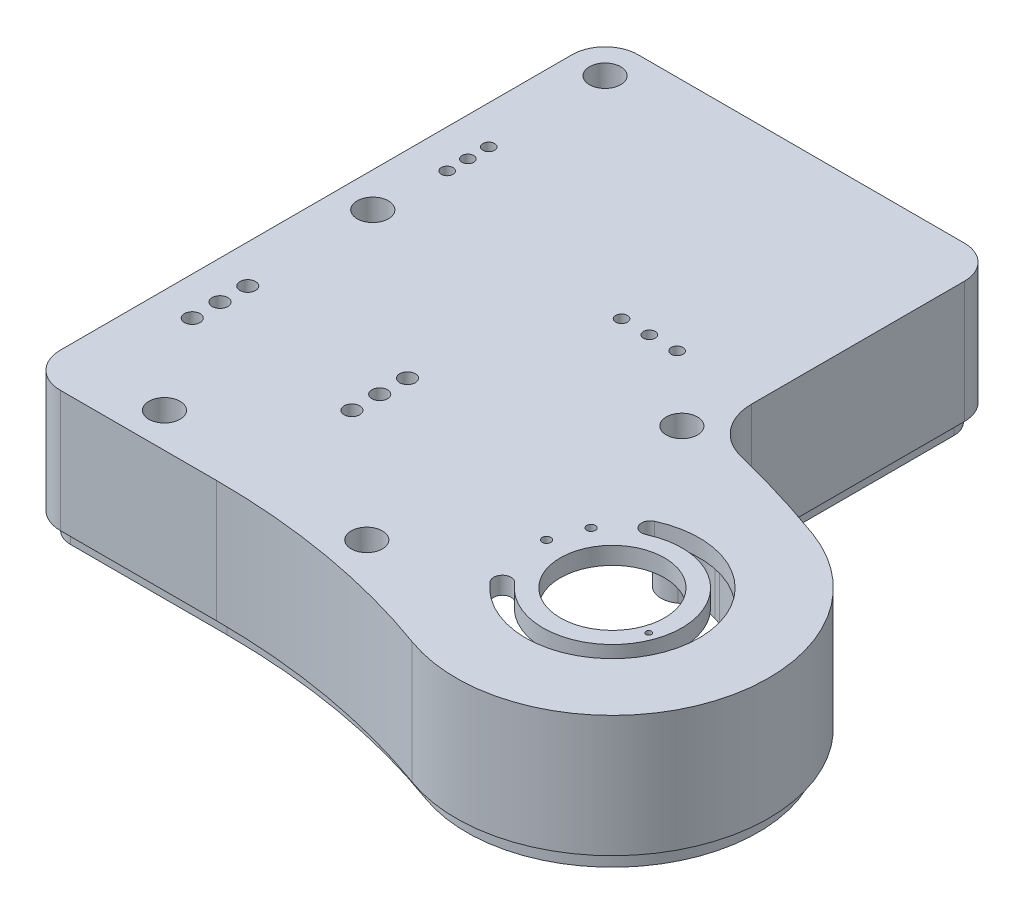
SolidWorks part; units mm, degrees
ref_plane "정면" through (0, 0, 0) normal (0, 0, 1) x (1, 0, 0)
ref_plane "윗면" through (0, 0, 0) normal (0, 1, 0) x (1, 0, 0)
ref_plane "우측면" through (0, 0, 0) normal (1, 0, 0) x (0, 0, -1)
sketch "스케치1" plane through (0, 0, 0) normal (0, 1, 0) x (1, 0, 0)
  line L0 (0, 0) -> (0, 23630.4906) construction
  line L1 (0, 0) -> (23630.4906, 0) construction
  line L2 (10, 1142.033) -> (10, 121.9) construction
  line L3 (10, -245) -> (78.404, -57.0615) construction
  line L4 (-35.5, 121.9) -> (10, 121.9)
  line L5 (-45, 112.4) -> (-45, -35)
  line L6 (-35, -45) -> (10, -45)
  line L9 (109.1858, 27.5109) -> (17111.0072, 46739.631) construction
  line L10 (10, 121.9) -> (58.5, 121.9)
  line L13 (68, 112.4) -> (68, 51.1351)
  line L14 (10, -45) -> (10, -23528.7236) construction
  arc A0 (78.404, -57.0615) -> (10, -45) centre (10, -245) ccw
  arc A2 (109.1858, 27.5109) -> (79.4098, 36.5711) centre (10, -245) ccw
  arc A3 (78.404, -57.0615) -> (109.1858, 27.5109) centre (93.7949, -14.7753) ccw
  arc A4 (-35.5, 121.9) -> (-45, 112.4) centre (-35.5, 112.4) ccw
  arc A5 (-45, -35) -> (-35, -45) centre (-35, -35) ccw
  arc A6 (58.5, 121.9) -> (68, 112.4) centre (58.5, 112.4) cw
  arc A7 (68, 51.1351) -> (79.4098, 36.5711) centre (83, 51.1351) ccw
  point P19 (-45, 121.9)
  point P24 (-45, -45)
  point P27 (68, 121.9)
  dimension "D5" = 400
  dimension "D6" = 90
  dimension "D9" = 9.5
  dimension "D10" = 10
  dimension "D11" = 9.5
  dimension "D12" = 15
  dimension "D1" = 10
  dimension "D2" = 55
  dimension "D3" = 166.9
  dimension "D4" = 45
  dimension "D7" = 20
  dimension "D8" = 58
extrude "보스-돌출1" add sketch "스케치1" along normal blind 35
sketch "스케치2" plane through (0, 0, 0) normal (0, -1, 0) x (1, 0, 0)
  line L8 (-40, 35) -> (-40, -112.4)
  line L9 (-35.5, -116.9) -> (58.5, -116.9)
  line L10 (63, -112.4) -> (63, -51.1351)
  line L11 (10, 40) -> (-35, 40)
  line L12 (-40, 35) -> (-40, -112.4)
  line L13 (-35.5, -116.9) -> (58.5, -116.9)
  line L14 (63, -112.4) -> (63, -51.1351)
  line L15 (10, 40) -> (-35, 40)
  arc A5 (-35, 40) -> (-40, 35) centre (-35, 35) ccw
  arc A6 (78.2131, -31.7164) -> (107.4757, -22.8124) centre (10, 245) ccw
  arc A7 (107.4757, -22.8124) -> (80.1141, 52.363) centre (93.7949, 14.7753) ccw
  arc A8 (10, 40) -> (80.1141, 52.363) centre (10, 245) ccw
  arc A9 (78.2131, -31.7164) -> (107.4757, -22.8124) centre (10, 245) ccw
  arc A10 (107.4757, -22.8124) -> (80.1141, 52.363) centre (93.7949, 14.7753) ccw
  arc A11 (10, 40) -> (80.1141, 52.363) centre (10, 245) ccw
  arc A12 (-35, 40) -> (-40, 35) centre (-35, 35) ccw
  arc A13 (-40, -112.4) -> (-35.5, -116.9) centre (-35.5, -112.4) ccw
  arc A14 (-40, -112.4) -> (-35.5, -116.9) centre (-35.5, -112.4) ccw
  arc A16 (58.5, -116.9) -> (63, -112.4) centre (58.5, -112.4) ccw
  arc A18 (58.5, -116.9) -> (63, -112.4) centre (58.5, -112.4) ccw
  arc A20 (78.2131, -31.7164) -> (63, -51.1351) centre (83, -51.1351) ccw
  arc A21 (78.2131, -31.7164) -> (63, -51.1351) centre (83, -51.1351) ccw
  dimension "D1" = 5
extrude "컷-돌출1" cut sketch "스케치2" against normal blind 30
sketch "스케치3" plane through (0, 35, 0) normal (0, 1, 0) x (1, 0, 0)
  line L0 (93.7949, -14.7753) -> (17194.8021, 46969.8557) construction
  circle A0 centre (93.7949, -14.7753) radius 15
  dimension "D1" = 30
  dimension "D2" = 45
extrude "컷-돌출2" cut sketch "스케치3" against normal up to next
sketch "스케치4" plane through (0, 35, 0) normal (0, 1, 0) x (1, 0, 0)
  line L0 (93.7949, -14.7753) -> (17194.8021, 46969.8557) construction
  line L1 (93.7949, -14.7753) -> (47078.426, -17115.7825) construction
  line L2 (75.7667, 23.8863) -> (21206.6798, -45291.503) construction
  line L3 (93.7949, -14.7753) -> (-38208.4272, -32154.1558) construction
  arc A0 (78.474, -27.6311) -> (85.3426, 3.3508) centre (93.7949, -14.7753) ccw
  arc A1 (74.6438, -30.845) -> (83.2295, 7.8824) centre (93.7949, -14.7753) ccw
  arc A2 (83.2295, 7.8824) -> (85.3426, 3.3508) centre (84.286, 5.6166) ccw
  arc A3 (78.474, -27.6311) -> (74.6438, -30.845) centre (76.5589, -29.238) ccw
  point P16 (93.7949, -14.7753)
  dimension "D3" = 40
  dimension "D4" = 50
  dimension "D5" = 5
  dimension "D6" = 5
  dimension "D1" = 45
  dimension "D2" = 60
  dimension "D7" = 22.5
  dimension "D8" = 22.5
extrude "컷-돌출3" cut sketch "스케치4" against normal blind 10
sketch "스케치5" plane through (-45, 0, 0) normal (-1, 0, 0) x (0, 0, 1)
  line L0 (-112.4, 0) -> (35, 0) construction
  line L2 (0, 0) -> (35355.3391, 35355.3391) construction
  line L3 (35, 35) -> (35, 0) construction
  circle A0 centre (0, 0) radius 15
  circle A2 centre (-71.4, 0) radius 6.5
  dimension "D1" = 30
  dimension "D6" = 13
  dimension "D2" = 35
  dimension "D4" = 135
  dimension "D7" = 71.4
extrude "컷-돌출4" cut sketch "스케치5" against normal up to next
sketch "스케치10" plane through (0, 30, 0) normal (0, -1, 0) x (1, 0, 0)
  line L0 (14, -107.0597) -> (14, 49892.9403) construction
  line L2 (25.0446, -116.9) -> (85.2157, -116.9) construction
  line L3 (-35.5, -116.9) -> (58.5, -116.9) construction
  line L4 (-72.2684, -57.65) -> (49927.7316, -57.65) construction
  line L5 (101.8497, -53.65) -> (-49898.1503, -53.65) construction
  line L7 (36, -9.7194) -> (36, -50009.7194) construction
  line L8 (44, -4.2181) -> (44, -50004.2181) construction
  line L9 (28, -0.9172) -> (28, -50000.9172) construction
  circle A0 centre (28, -53.65) radius 1.7
  circle A1 centre (36, -53.65) radius 1.7
  circle A2 centre (44, -53.65) radius 1.7
  dimension "D7" = 3.4
  dimension "D8" = 3.4
  dimension "D9" = 3.4
  dimension "D1" = 59.25
  dimension "D3" = 4
  dimension "D4" = 14
  dimension "D5" = 22
  dimension "D6" = 30
extrude "컷-돌출7" cut sketch "스케치10" against normal up to next
sketch "스케치11" plane through (0, 30, 0) normal (0, -1, 0) x (1, 0, 0)
  line L0 (93.7949, 14.7753) -> (-17007.2122, 46999.4063) construction
  line L1 (93.7949, 14.7753) -> (47078.426, 17115.7825) construction
  circle A0 centre (110.2396, 20.7607) radius 1
  circle A2 centre (72.3513, 12.2913) radius 1.5
  circle A3 centre (75.7715, 2.8944) radius 1.5
  dimension "D1" = 2
  dimension "D2" = 3
  dimension "D4" = 3
  dimension "D3" = 17.5
  dimension "D5" = 5
  dimension "D6" = 5
  dimension "D7" = 21
  dimension "D8" = 21
sketch "스케치13" plane through (0, 30, 0) normal (0, -1, 0) x (1, 0, 0)
  line L0 (-45, -27.7843) -> (-45, 49972.2157) construction
  line L2 (-28.5635, -121.9) -> (-50028.5635, -121.9) construction
  line L4 (-26.7948, 45) -> (-50026.7948, 45) construction
  line L6 (67.3239, -38.7149) -> (31158.5874, 39119.0855) construction
  line L7 (45.5979, 43.1144) -> (49285.9855, 8725.5233) construction
  line L8 (45.5979, 43.1144) -> (-8636.811, 49283.5021) construction
  line L9 (66.2527, -37.8643) -> (-39091.5478, 31053.3992) construction
  line L10 (-96.5207, -45) -> (49903.4793, -45) construction
  arc A1 (10, 40) -> (80.1141, 52.363) centre (10, 245) ccw construction
  arc A2 (78.2131, -31.7164) -> (63, -51.1351) centre (83, -51.1351) ccw construction
  circle A3 centre (-15, 35) radius 6
  circle A4 centre (-35, -45) radius 6
  circle A5 centre (-35, -111.9) radius 6
  circle A6 centre (63.4081, -35.6058) radius 6
  circle A7 centre (46.4661, 38.1904) radius 6
  point P17 (45.5979, 43.1144)
  dimension "D2" = 12
  dimension "D5" = 12
  dimension "D7" = 12
  dimension "D10" = 12
  dimension "D12" = 12
  dimension "D1" = 90
  dimension "D3" = 10
  dimension "D4" = 30
  dimension "D6" = 10
  dimension "D8" = 10
  dimension "D9" = 10
  dimension "D11" = 5
  dimension "D13" = 5
extrude "보스-돌출2" add sketch "스케치13" along normal blind 35
sketch "스케치14" plane through (0, 0, 0) normal (0, -1, 0) x (1, 0, 0)
  line L8 (-42, 35) -> (-42, 15)
  line L9 (-42, 35) -> (-42, 15)
  line L10 (-42, 15) -> (-40, 15)
  line L11 (-40, 35) -> (-40, 15)
  line L12 (-40, 35) -> (-40, 15)
  line L17 (65, -51.1351) -> (65, -112.4)
  line L18 (-35, 42) -> (10, 42)
  line L19 (65, -51.1351) -> (65, -112.4)
  line L20 (-35, 42) -> (10, 42)
  line L31 (63, -51.1351) -> (63, -112.4)
  line L32 (-35, 40) -> (10, 40)
  line L33 (63, -51.1351) -> (63, -112.4)
  line L34 (-35, 40) -> (10, 40)
  line L37 (-40, -64.9) -> (-40, -15)
  line L38 (-40, -64.9) -> (-40, -15)
  line L40 (-42, -64.9) -> (-42, -15)
  line L41 (-42, -64.9) -> (-42, -15)
  line L47 (58.5, -118.9) -> (-35.5, -118.9)
  line L48 (-42, -112.4) -> (-42, -77.9)
  line L49 (58.5, -118.9) -> (-35.5, -118.9)
  line L50 (-42, -112.4) -> (-42, -77.9)
  line L54 (-42, -77.9) -> (-40, -77.9)
  line L55 (58.5, -116.9) -> (-35.5, -116.9)
  line L56 (-40, -112.4) -> (-40, -77.9)
  line L57 (58.5, -116.9) -> (-35.5, -116.9)
  line L58 (-40, -112.4) -> (-40, -77.9)
  line L59 (-42, -64.9) -> (-40, -64.9)
  line L60 (-42, -15) -> (-40, -15)
  arc A16 (58.5, -118.9) -> (65, -112.4) centre (58.5, -112.4) ccw
  arc A17 (58.5, -118.9) -> (65, -112.4) centre (58.5, -112.4) ccw
  arc A19 (58.5, -116.9) -> (63, -112.4) centre (58.5, -112.4) ccw
  arc A20 (58.5, -116.9) -> (63, -112.4) centre (58.5, -112.4) ccw
  arc A37 (78.6918, -33.6583) -> (65, -51.1351) centre (83, -51.1351) ccw
  arc A38 (78.6918, -33.6583) -> (108.1598, -24.6918) centre (10, 245) ccw
  arc A39 (108.1598, -24.6918) -> (79.4301, 54.2424) centre (93.7949, 14.7753) ccw
  arc A40 (10, 42) -> (79.4301, 54.2424) centre (10, 245) ccw
  arc A41 (78.6918, -33.6583) -> (65, -51.1351) centre (83, -51.1351) ccw
  arc A42 (78.6918, -33.6583) -> (108.1598, -24.6918) centre (10, 245) ccw
  arc A43 (108.1598, -24.6918) -> (79.4301, 54.2424) centre (93.7949, 14.7753) ccw
  arc A44 (10, 42) -> (79.4301, 54.2424) centre (10, 245) ccw
  arc A46 (-35, 42) -> (-42, 35) centre (-35, 35) ccw
  arc A47 (-35, 42) -> (-42, 35) centre (-35, 35) ccw
  arc A71 (-42, -112.4) -> (-35.5, -118.9) centre (-35.5, -112.4) ccw
  arc A72 (-42, -112.4) -> (-35.5, -118.9) centre (-35.5, -112.4) ccw
  arc A73 (78.2131, -31.7164) -> (63, -51.1351) centre (83, -51.1351) ccw
  arc A74 (78.2131, -31.7164) -> (107.4757, -22.8124) centre (10, 245) ccw
  arc A75 (107.4757, -22.8124) -> (80.1141, 52.363) centre (93.7949, 14.7753) ccw
  arc A76 (10, 40) -> (80.1141, 52.363) centre (10, 245) ccw
  arc A77 (-35, 40) -> (-40, 35) centre (-35, 35) ccw
  arc A78 (78.2131, -31.7164) -> (63, -51.1351) centre (83, -51.1351) ccw
  arc A79 (78.2131, -31.7164) -> (107.4757, -22.8124) centre (10, 245) ccw
  arc A80 (107.4757, -22.8124) -> (80.1141, 52.363) centre (93.7949, 14.7753) ccw
  arc A81 (10, 40) -> (80.1141, 52.363) centre (10, 245) ccw
  arc A82 (-35, 40) -> (-40, 35) centre (-35, 35) ccw
  arc A85 (-40, -112.4) -> (-35.5, -116.9) centre (-35.5, -112.4) ccw
  arc A86 (-40, -112.4) -> (-35.5, -116.9) centre (-35.5, -112.4) ccw
  dimension "D1" = 3
  dimension "D2" = 3
  dimension "D3" = 5
  dimension "D4" = 5
  dimension "D5" = 3
  dimension "D6" = 3
  dimension "D7" = 5
  dimension "D8" = 2
  dimension "D9" = 0
  dimension "D10" = 2
  dimension "D11" = 0
extrude "보스-돌출3" add sketch "스케치14" along normal blind 5
fillet "필렛1" radius 10 10 edges at (-18.3166, 12.5, 40) (-11.6834, 12.5, 40) (-40, 12.5, -48.3166) (-40, 12.5, -41.6834) (-31.6834, 12.5, -116.9) (-40, 12.5, -108.5834) (69.3365, 12.5, -36.53) (65.6613, 12.5, -41.1667) (42.3663, 12.5, 42.5712) (48.8203, 12.5, 43.7092)
sketch "스케치18" plane through (0, 35, 0) normal (0, 1, 0) x (1, 0, 0)
  line L0 (-45, 31.9538) -> (-45, 50031.9538) construction
  line L2 (-19.837, 121.9) -> (-50019.837, 121.9) construction
  line L4 (-2.2619, -45) -> (-50002.2619, -45) construction
  line L6 (44.7296, -48.0384) -> (49285.1173, -8730.4473) construction
  line L7 (44.7296, -48.0384) -> (8727.1385, 49192.3492) construction
  line L8 (71.2397, 41.824) -> (31162.5032, -39115.9764) construction
  line L9 (70.1684, 40.9735) -> (39227.9689, 31132.237) construction
  line L10 (-176.4392, 45) -> (49823.5608, 45) construction
  arc A0 (78.404, -57.0615) -> (10, -45) centre (10, -245) ccw construction
  circle A2 centre (-35, 111.9) radius 2.25
  circle A3 centre (-35, 45) radius 2.25
  circle A4 centre (-15, -35) radius 2.25
  circle A5 centre (63.4081, 35.6058) radius 2.25
  circle A6 centre (46.4661, -38.1904) radius 2.25
  arc A7 (68, 51.1351) -> (79.4098, 36.5711) centre (83, 51.1351) ccw construction
  point P11 (44.7296, -48.0384)
  dimension "D1" = 4.5
  dimension "D2" = 4.5
  dimension "D7" = 4.5
  dimension "D10" = 4.5
  dimension "D12" = 4.5
  dimension "D3" = 10
  dimension "D4" = 10
  dimension "D5" = 90
  dimension "D6" = 10
  dimension "D8" = 10
  dimension "D9" = 30
  dimension "D11" = 10
  dimension "D13" = 10
sketch "스케치22" plane through (0, 35, 0) normal (0, 1, 0) x (1, 0, 0)
  line L0 (-45, 23.2625) -> (-45, 50023.2625) construction
  line L2 (-45, -35) -> (49955, -35) construction
  line L3 (-64.5514, 0) -> (49935.4486, 0) construction
  line L4 (12, 34.6091) -> (12, -49965.3909) construction
  line L5 (-75.8764, 71.4) -> (49924.1236, 71.4) construction
  line L6 (-34, 39.0133) -> (-34, -49960.9867) construction
  circle A0 centre (-34, 71.4) radius 1.7
  circle A1 centre (-34, 65.4) radius 1.7
  circle A2 centre (-34, 77.4) radius 1.7
  circle A3 centre (12, 8) radius 2.25
  circle A4 centre (12, 0) radius 2.25
  circle A5 centre (12, -8) radius 2.25
  dimension "D5" = 3.4
  dimension "D6" = 3.4
  dimension "D7" = 3.4
  dimension "D8" = 4.5
  dimension "D9" = 4.5
  dimension "D10" = 4.5
  dimension "D1" = 35
  dimension "D2" = 57
  dimension "D3" = 106.4
  dimension "D4" = 11
  dimension "D11" = 6
  dimension "D12" = 6
  dimension "D13" = 8
  dimension "D14" = 8
extrude "컷-돌출15" cut sketch "스케치22" against normal up to next
sketch "스케치23" plane through (0, 35, 0) normal (0, 1, 0) x (1, 0, 0)
  line L0 (12, 8) -> (-49988, 8) construction
  line L1 (12, 0) -> (-49988, 0) construction
  line L2 (12, -8) -> (-49988, -8) construction
  line L3 (-34, 7.9994) -> (-34, 50007.9994) construction
  circle A0 centre (-34, -8) radius 2.25
  circle A1 centre (-34, 8) radius 2.25
  circle A2 centre (-34, 0) radius 2.25
  point P18 (0, 0)
  point P19 (0, 0)
  point P20 (0, 0)
  dimension "D1" = 4.5
  dimension "D2" = 4.5
  dimension "D3" = 4.5
extrude "컷-돌출16" cut sketch "스케치23" against normal through all
sketch "스케치24" plane through (0, 0, -121.9) normal (0, 0, -1) x (-1, 0, 0)
  line L0 (-68, 13.3834) -> (-68, 50013.3834) construction
  line L2 (-68, 35) -> (-68, 0) construction
  line L3 (-63, 54.0832) -> (-63, -49945.9168) construction
  line L4 (-90.8305, 10) -> (49909.1695, 10) construction
  line L5 (-58.5, 0) -> (35.5, 0) construction
  circle A0 centre (-44, 10) radius 1.2
  circle A1 centre (-28, 10) radius 1.2
  point P14 (0, 0)
  point P15 (0, 0)
  dimension "D3" = 2.4
  dimension "D4" = 2.4
  dimension "D1" = 5
  dimension "D2" = 10
  dimension "D5" = 19
  dimension "D6" = 35
extrude "컷-돌출17" cut sketch "스케치24" against normal up to next
hole_wizard "M4 남비 머리 나사용 카운터보어1" positions "스케치25" profile "스케치26" counterbore size "M4" standard "ISO"
sketch "스케치25" plane through (0, 35, 0) normal (0, 1, 0) x (1, 0, 0)
  point P0 (-35, 111.9)
  point P3 (63.4081, 35.6058)
  point P6 (-35, 45)
  point P9 (-15, -35)
  point P12 (46.4661, -38.1904)
sketch "스케치26" plane through (-35, 35, -111.9) normal (1, 0, 0) x (0, 0, 1)
  line L0 (0, 0) -> (0, 41.3519)
  line L1 (0, 41.3519) -> (2.25, 40)
  line L2 (2.25, 40) -> (2.25, 33.1)
  line L3 (2.25, 33.1) -> (4.5, 33.1)
  line L4 (4.5, 33.1) -> (4.5, 0)
  line L5 (4.5, 0) -> (0, 0)
  line L10 (0, 41.3519) -> (-2.25, 40) construction
  line L11 (0, -6.35) -> (0, 107.95) construction
  dimension "구멍 지름" = 4.5
  dimension "구멍 깊이" = 40
  dimension "카운터보어 지름" = 9
  dimension "카운터보어 깊이" = 33.1
  dimension "드릴 각도" = 118
hole_wizard "M2 나사 구멍1" positions "스케치27" profile "스케치28" tap size "M2" standard "ISO"
sketch "스케치27" plane through (0, 30, 0) normal (0, -1, 0) x (-1, 0, 0)
  point P0 (-110.2396, -20.7607)
sketch "스케치28" plane through (110.2396, 30, 20.7607) normal (1, 0, 0) x (0, 0, -1)
  line L0 (0, 0) -> (0, 6.4807)
  line L1 (0, 6.4807) -> (0.8, 6)
  line L2 (0.8, 6) -> (0.8, 0)
  line L5 (0.8, 0) -> (0, 0)
  line L10 (0, 6.4807) -> (-0.8, 6) construction
  line L11 (0, -6.35) -> (0, 107.95) construction
  dimension "탭 드릴 지름" = 1.6
  dimension "탭 드릴 깊이" = 6
  dimension "드릴 각도" = 118
cosmetic thread "구멍 나사산1" parameters "D1"=4, "D2"=2
hole_wizard "M3 나사 구멍1" positions "스케치29" profile "스케치30" tap size "M3" standard "ISO"
sketch "스케치29" plane through (0, 30, 0) normal (0, -1, 0) x (-1, 0, 0)
  point P0 (-75.7715, -2.8944)
  point P3 (-72.3513, -12.2913)
sketch "스케치30" plane through (75.7715, 30, 2.8944) normal (1, 0, 0) x (0, 0, -1)
  line L0 (0, 0) -> (0, 9.2511)
  line L1 (0, 9.2511) -> (1.25, 8.5)
  line L2 (1.25, 8.5) -> (1.25, 0)
  line L5 (1.25, 0) -> (0, 0)
  line L10 (0, 9.2511) -> (-1.25, 8.5) construction
  line L11 (0, -6.35) -> (0, 107.95) construction
  dimension "탭 드릴 지름" = 2.5
  dimension "탭 드릴 깊이" = 8.5
  dimension "드릴 각도" = 118
cosmetic thread "구멍 나사산2" parameters "D1"=5, "D2"=3
cosmetic thread "구멍 나사산3" parameters "D1"=5, "D2"=3
